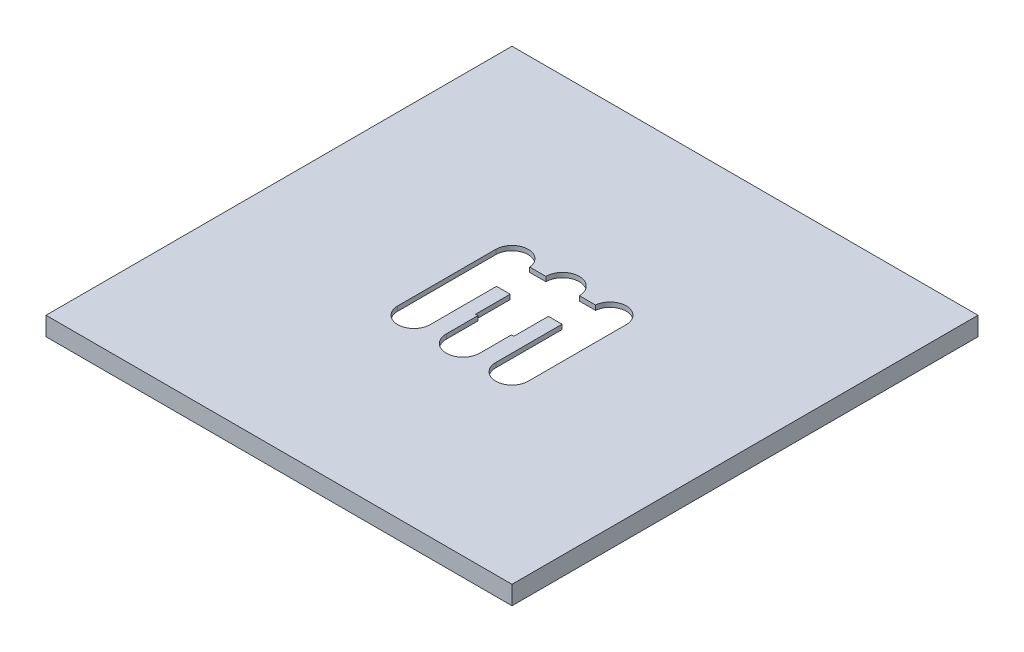
SolidWorks part; units mm, degrees
ref_plane "Front Plane" through (0, 0, 0) normal (0, 0, 1) x (1, 0, 0)
ref_plane "Top Plane" through (0, 0, 0) normal (0, 1, 0) x (1, 0, 0)
ref_plane "Right Plane" through (0, 0, 0) normal (1, 0, 0) x (0, 0, -1)
sketch "Sketch1" plane through (0, 0, 0) normal (0, 1, 0) x (1, 0, 0)
  line L0 (-48, 48) -> (-48, -48)
  line L1 (50, 50) -> (-50, 50)
  line L2 (50, 50) -> (50, -50)
  line L3 (50, -50) -> (-50, -50)
  line L4 (-50, 50) -> (-50, -50)
  line L5 (50, 50) -> (-50, -50) construction
  line L6 (50, -50) -> (-50, 50) construction
  line L7 (48, -48) -> (-48, -48)
  line L8 (48, 48) -> (48, -48)
  line L9 (48, 48) -> (-48, 48)
  point P0 (0, 0)
  dimension "D1" = 100
  dimension "D2" = 100
  dimension "D3" = 2
extrude "Boss-Extrude1" add sketch "Sketch1" along normal blind 3
sketch "Sketch2" plane through (0, 3, 0) normal (0, 1, 0) x (1, 0, 0)
  line L0 (-50, -50) -> (50, -50) construction
  line L1 (50, -50) -> (50, 50) construction
  line L2 (50, 50) -> (-50, 50) construction
  line L3 (-50, 50) -> (-50, -50) construction
  line L4 (-50, -50) -> (50, -50)
  line L5 (50, -50) -> (50, 50)
  line L6 (50, 50) -> (-50, 50)
  line L7 (-50, 50) -> (-50, -50)
extrude "Boss-Extrude2" add sketch "Sketch2" along normal blind 1
sketch "Sketch3" plane through (0, 3, 0) normal (0, -1, 0) x (1, 0, 0)
  line L0 (-10.5174, 10.5174) -> (-10.5174, -10.5174) construction
  line L1 (15, 15) -> (-15, 15)
  line L2 (15, 15) -> (15, -15)
  line L3 (15, -15) -> (-15, -15)
  line L4 (-15, 15) -> (-15, -15)
  line L5 (15, 15) -> (-15, -15) construction
  line L6 (15, -15) -> (-15, 15) construction
  line L7 (-7.0348, 10.5174) -> (-7.0348, -10.5174)
  line L8 (-14, 10.5174) -> (-14, -10.5174)
  line L9 (0, -2.2) -> (0, 2.2) construction
  line L10 (10.5174, 10.5174) -> (10.5174, -10.5174) construction
  line L11 (7.0348, 10.5174) -> (7.0348, -10.5174)
  line L12 (14, 10.5174) -> (14, -10.5174)
  line L13 (-10.5174, -7.2832) -> (10.5174, -7.2832) construction
  line L14 (-10.5174, -3.7091) -> (10.5174, -3.7091)
  line L15 (-10.5174, -10.8573) -> (10.5174, -10.8573)
  line L16 (0, 10.5174) -> (0, -10.8573) construction
  line L17 (4.1048, 3.7091) -> (-4.1048, 3.7091)
  line L18 (4.1048, 3.7091) -> (4.1048, -3.7091)
  line L19 (4.1048, -3.7091) -> (-4.1048, -3.7091)
  line L20 (-4.1048, 3.7091) -> (-4.1048, -3.7091)
  line L21 (4.1048, 3.7091) -> (-4.1048, -3.7091) construction
  line L22 (4.1048, -3.7091) -> (-4.1048, 3.7091) construction
  line L23 (3.5916, 10.5174) -> (3.5916, -10.8573)
  line L24 (-3.5916, 10.5174) -> (-3.5916, -10.8573)
  arc A0 (-7.0348, 10.5174) -> (-14, 10.5174) centre (-10.5174, 10.5174) ccw
  arc A1 (-14, -10.5174) -> (-7.0348, -10.5174) centre (-10.5174, -10.5174) ccw
  arc A2 (7.0348, 10.5174) -> (14, 10.5174) centre (10.5174, 10.5174) cw
  arc A3 (14, -10.5174) -> (7.0348, -10.5174) centre (10.5174, -10.5174) cw
  arc A4 (-10.5174, -3.7091) -> (-10.5174, -10.8573) centre (-10.5174, -7.2832) ccw
  arc A5 (10.5174, -10.8573) -> (10.5174, -3.7091) centre (10.5174, -7.2832) ccw
  arc A6 (3.5916, 10.5174) -> (-3.5916, 10.5174) centre (0, 10.5174) ccw
  arc A7 (-3.5916, -10.8573) -> (3.5916, -10.8573) centre (0, -10.8573) ccw
  point P0 (0, 0)
  point P8 (-10.5174, 0)
  point P13 (-10.5174, 14)
  point P14 (-10.5174, -14)
  point P19 (10.5174, 0)
  point P26 (0, -7.2832)
  point P31 (0, 0)
  point P38 (0, -0.17)
  dimension "D1" = 30
  dimension "D2" = 30
  dimension "D3" = 28
extrude "Cut-Extrude1" cut sketch "Sketch3" against normal blind 1 contours L15 A5 L12 L14 L11 A3 | A5 L15 A3 L12 | L15 A3 L11 L14 L7 A1 | L14 A4 L8 L15 A1 L7 | A4 L8 A1 L15 | A4 L14 L7 A0 L8 | L17 L20 L14 L18 | L15 A7 | L17 L24 L19 L23 | L17 L23 L19 L18 | L23 A6 L24 L17 | L15 A3 L11 L14 L19 L23 | L19 L24 L15 L23 | A5 L12 A2 L11 L14
